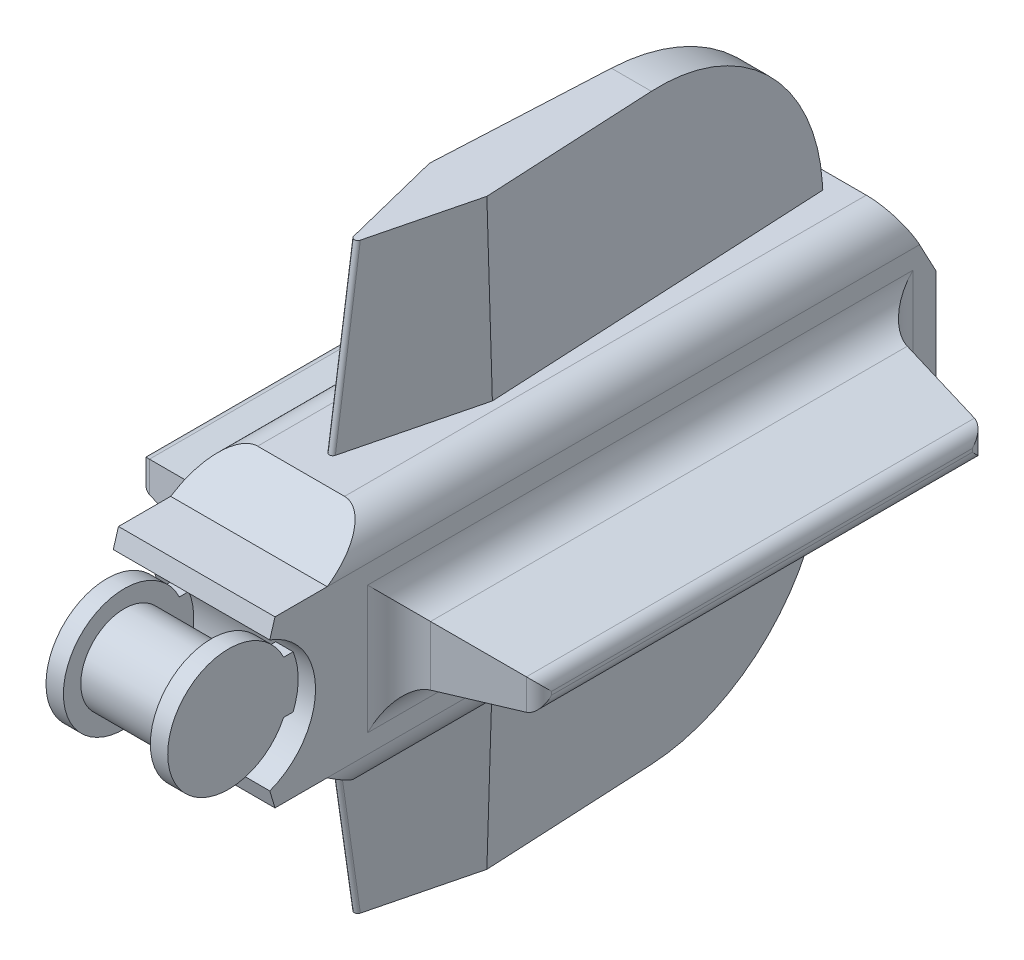
SolidWorks part; units mm, degrees
ref_plane "Front Plane" through (0, 0, 0) normal (0, 0, 1) x (1, 0, 0)
ref_plane "Top Plane" through (0, 0, 0) normal (0, 1, 0) x (1, 0, 0)
ref_plane "Right Plane" through (0, 0, 0) normal (1, 0, 0) x (0, 0, -1)
sketch "Sketch1" plane through (0, 0, 0) normal (1, 0, 0) x (0, 0, -1)
  circle A0 centre (0, 0) radius 3.175
  dimension "D1" = 6.35
extrude "Boss-Extrude1" add sketch "Sketch1" along normal mid plane 6.35
sketch "Sketch2" plane through (3.175, 0, 0) normal (1, 0, 0) x (0, 0, -1)
  circle A0 centre (0, 0) radius 4.445
  dimension "D1" = 8.89
extrude "Boss-Extrude2" add sketch "Sketch2" along normal blind 1.27
mirror "Mirror1" about plane through (0, 0, 0) normal (1, 0, 0) of "Boss-Extrude2"
sketch "Sketch3" plane through (4.445, 0, 0) normal (1, 0, 0) x (0, 0, -1)
  line L1 (0, 1.905) -> (6.35, 1.905)
  line L2 (0, 1.905) -> (0, -1.905)
  line L3 (0, -1.905) -> (6.35, -1.905)
  line L4 (6.35, 1.905) -> (6.35, -1.905)
  point P4 (0, 0)
  dimension "D1" = 3.81
  dimension "D2" = 6.35
extrude "Boss-Extrude3" add sketch "Sketch3" against normal blind 1.27
mirror "Mirror2" about plane through (0, 0, 0) normal (1, 0, 0) of "Boss-Extrude3"
sketch "Sketch4" plane through (-3.175, 0, 0) normal (1, 0, 0) x (0, 0, -1)
  line L0 (1.7375, 4.7736) -> (0, 0) construction
  line L1 (0, 0) -> (5.08, 0) construction
  line L2 (1.7375, 4.7736) -> (2.1185, 6.0436)
  line L3 (2.1185, 6.0436) -> (5.9285, 6.0436)
  line L4 (0, 0) -> (1.7375, -4.7736) construction
  line L5 (5.9285, 6.0436) -> (9.7385, 8.5836)
  line L6 (9.7385, 8.5836) -> (47.8385, 8.5836)
  line L7 (47.8385, 8.5836) -> (50.3785, 3.81)
  line L8 (50.3785, 3.81) -> (50.3785, -3.81)
  line L9 (50.3785, 0) -> (5.08, 0) construction
  line L10 (47.8385, -8.5836) -> (50.3785, -3.81)
  line L11 (9.7385, -8.5836) -> (47.8385, -8.5836)
  line L12 (5.9285, -6.0436) -> (9.7385, -8.5836)
  line L13 (2.1185, -6.0436) -> (5.9285, -6.0436)
  line L14 (1.7375, -4.7736) -> (2.1185, -6.0436)
  arc A0 (1.7375, 4.7736) -> (1.7375, -4.7736) centre (0, 0) cw
  dimension "D1" = 5.08
  dimension "D2" = 140
  dimension "D3" = 1.27
  dimension "D4" = 0.381
  dimension "D5" = 3.81
  dimension "D6" = 3.81
  dimension "D7" = 2.54
  dimension "D8" = 38.1
  dimension "D9" = 7.62
  dimension "D10" = 2.54
extrude "Boss-Extrude4" add sketch "Sketch4" against normal blind 2.54 and the other way blind 8.89
sketch "Sketch5" plane through (0, 0, -50.3785) normal (0, 0, -1) x (-1, 0, 0)
  circle A0 centre (0, 0) radius 3.175
  dimension "D1" = 6.35
extrude "Cut-Extrude1" cut sketch "Sketch5" against normal blind 12.7
fillet "Fillet1" radius 2.54 4 edges at (5.715, -8.5836, -28.7885) (-5.715, -8.5836, -28.7885) (-5.715, 8.5836, -28.7885) (5.715, 8.5836, -28.7885)
sketch "Sketch6" plane through (5.715, 0, 0) normal (1, 0, 0) x (0, 0, -1)
  line L0 (50.3785, -3.81) -> (50.3785, 3.81) construction
  line L1 (11.0085, 2.54) -> (46.5685, 2.54)
  line L2 (11.0085, 2.54) -> (11.0085, -2.54)
  line L3 (11.0085, -2.54) -> (46.5685, -2.54)
  line L4 (46.5685, 2.54) -> (46.5685, -2.54)
  point P4 (11.0085, 0)
  point P6 (50.3785, 0)
  dimension "D1" = 3.81
  dimension "D2" = 5.08
  dimension "D3" = 35.56
extrude "Boss-Extrude5" add sketch "Sketch6" along normal blind 8.89 draft 10
mirror "Mirror3" about plane through (0, 0, 0) normal (1, 0, 0) of "Boss-Extrude5"
fillet "Fillet2" radius 1.016 8 edges at (-14.605, -0.9725, -28.7885) (-14.605, 0, -45.0009) (-14.605, 0.9725, -28.7885) (-14.605, 0, -12.576) (14.605, 0.9725, -28.7885) (14.605, 0, -45.0009) (14.605, -0.9725, -28.7885) (14.605, 0, -12.576)
fillet "Fillet3" radius 2.54 8 edges at (5.715, -2.54, -28.7885) (5.715, 0, -11.0085) (5.715, 0, -46.5685) (5.715, 2.54, -28.7885) (-5.715, 0, -11.0085) (-5.715, 0, -46.5685) (-5.715, -2.54, -28.7885) (-5.715, 2.54, -28.7885)
sketch "Sketch7" plane through (0, 8.5836, 0) normal (0, 1, 0) x (1, 0, 0)
  line L0 (0, 9.7385) -> (0, 47.8385) construction
  line L1 (3.175, 9.7385) -> (-3.175, 9.7385) construction
  line L2 (3.175, 47.8385) -> (-3.175, 47.8385) construction
  line L3 (-1.27, 46.5685) -> (1.27, 46.5685)
  line L4 (1.27, 46.5685) -> (2.54, 21.1685)
  line L5 (2.54, 21.1685) -> (0, 11.0085)
  line L6 (0, 11.0085) -> (-2.54, 21.1685)
  line L7 (-2.54, 21.1685) -> (-1.27, 46.5685)
  point P8 (0, 46.5685)
  dimension "D1" = 2.54
  dimension "D2" = 1.27
  dimension "D3" = 1.27
  dimension "D4" = 2.54
  dimension "D5" = 25.4
extrude "Boss-Extrude6" add sketch "Sketch7" along normal blind 12.7 draft 2
mirror "Mirror4" about plane through (0, 0, 0) normal (0, 1, 0) of "Boss-Extrude6"
fillet "Fillet4" radius 0.254 2 edges at (0, -14.9336, -11.9227) (0, 14.9336, -11.9227)
fillet "Fillet5" radius 12.7 2 edges at (0, -21.2836, -46.125) (0, 21.2836, -46.125)
